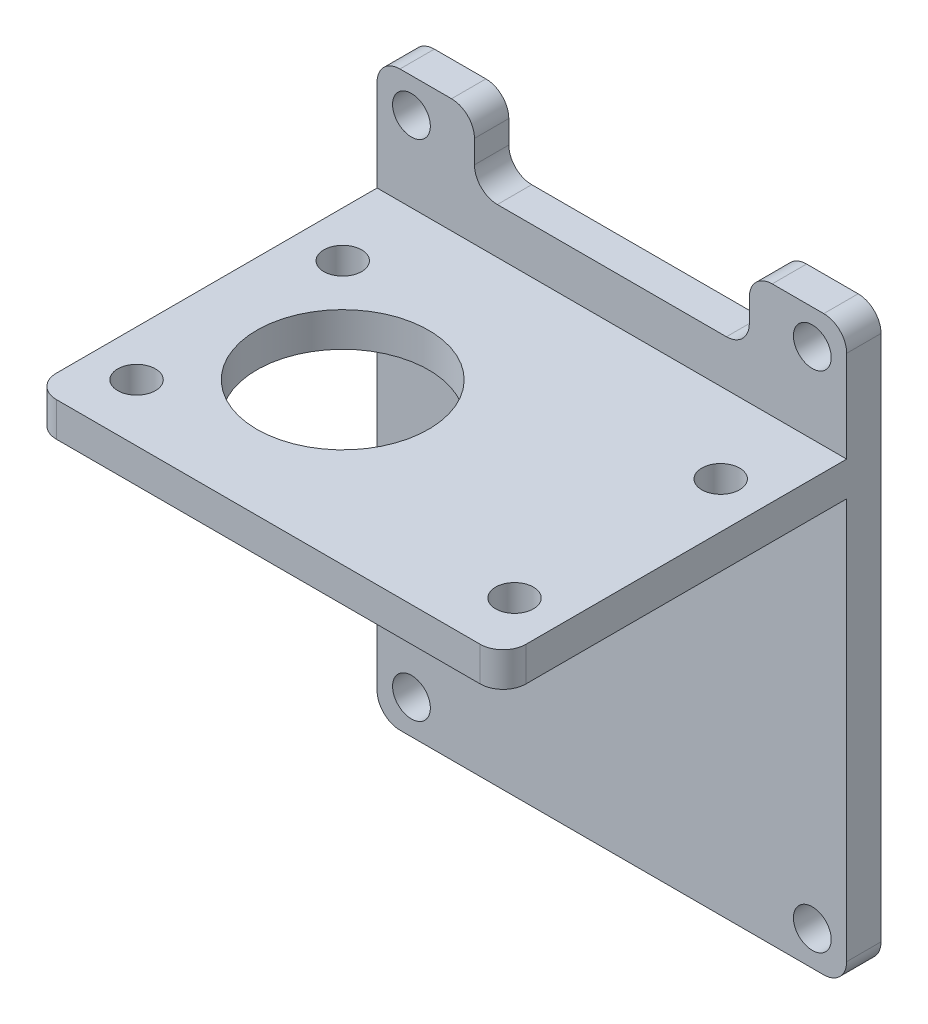
SolidWorks part; units mm, degrees
ref_plane "Front Plane" through (0, 0, 0) normal (0, 0, 1) x (1, 0, 0)
ref_plane "Top Plane" through (0, 0, 0) normal (0, 1, 0) x (1, 0, 0)
ref_plane "Right Plane" through (0, 0, 0) normal (1, 0, 0) x (0, 0, -1)
sketch "Sketch1" plane through (0, 0, 0) normal (0, 0, 1) x (1, 0, 0)
  line L0 (-3, 47) -> (38, 47)
  line L1 (0, 0) -> (35, 0) construction
  line L2 (0, 0) -> (0, 44) construction
  line L3 (0, 44) -> (35, 44) construction
  line L4 (35, 0) -> (35, 44) construction
  line L5 (38, -3) -> (38, 47)
  line L6 (-3, -3) -> (38, -3)
  line L7 (-3, -3) -> (-3, 47)
  circle A0 centre (0, 44) radius 1.65
  circle A1 centre (35, 44) radius 1.65
  circle A2 centre (35, 0) radius 1.65
  circle A3 centre (0, 0) radius 1.65
  dimension "D4" = 3.3
  dimension "D1" = 35
  dimension "D2" = 44
  dimension "D3" = 3
extrude "Boss-Extrude1" add sketch "Sketch1" along normal blind 3
sketch "Sketch2" plane through (0, 0, 3) normal (0, 0, 1) x (1, 0, 0)
  line L0 (-3, 47) -> (-3, -3) construction
  line L1 (-3, 37) -> (38, 37)
  line L2 (-3, 37) -> (-3, 34)
  line L3 (-3, 34) -> (38, 34)
  line L4 (38, 37) -> (38, 34)
  line L5 (38, -3) -> (38, 47) construction
  line L6 (38, 47) -> (-3, 47) construction
  dimension "D1" = 3
  dimension "D2" = 10
extrude "Boss-Extrude2" add sketch "Sketch2" along normal blind 30
sketch "Sketch3" plane through (0, 37, 0) normal (0, 1, 0) x (1, 0, 0)
  line L0 (17.5, -33) -> (17.5, -3) construction
  line L1 (38, -33) -> (-3, -33) construction
  line L2 (38, -3) -> (-3, -3) construction
  line L3 (1, -19) -> (10, -19) construction
  line L4 (1, -10) -> (34, -10) construction
  line L5 (1, -10) -> (1, -28) construction
  line L6 (1, -28) -> (34, -28) construction
  line L7 (34, -10) -> (34, -28) construction
  line L8 (1, -10) -> (34, -28) construction
  line L9 (1, -28) -> (34, -10) construction
  circle A0 centre (34, -28) radius 1.65
  circle A1 centre (34, -10) radius 1.65
  circle A2 centre (1, -10) radius 1.65
  circle A3 centre (1, -28) radius 1.65
  circle A4 centre (10, -19) radius 7.5
  point P6 (17.5, -19)
  dimension "D1" = 3.3
  dimension "D5" = 15
  dimension "D2" = 33
  dimension "D3" = 18
  dimension "D4" = 7
  dimension "D6" = 9
extrude "Cut-Extrude1" cut sketch "Sketch3" against normal blind 35
sketch "Sketch4" plane through (0, 0, 3) normal (0, 0, 1) x (1, 0, 0)
  line L0 (17.5, 44) -> (17.5, 47) construction
  line L1 (38, 47) -> (-3, 47) construction
  line L4 (5.5, 41) -> (29.5, 41)
  line L5 (5.5, 41) -> (5.5, 47)
  line L6 (5.5, 47) -> (29.5, 47)
  line L7 (29.5, 41) -> (29.5, 47)
  line L8 (5.5, 41) -> (29.5, 47) construction
  line L9 (5.5, 47) -> (29.5, 41) construction
  point P6 (17.5, 44)
  dimension "D1" = 24
  dimension "D2" = 6
extrude "Cut-Extrude2" cut sketch "Sketch4" against normal blind 10
fillet "Fillet2" radius 2 10 edges at (38, 35.5, 33) (-3, 35.5, 33) (38, -3, 1.5) (-3, -3, 1.5) (-3, 47, 1.5) (5.5, 47, 1.5) (5.5, 41, 1.5) (29.5, 41, 1.5) (29.5, 47, 1.5) (38, 47, 1.5)
